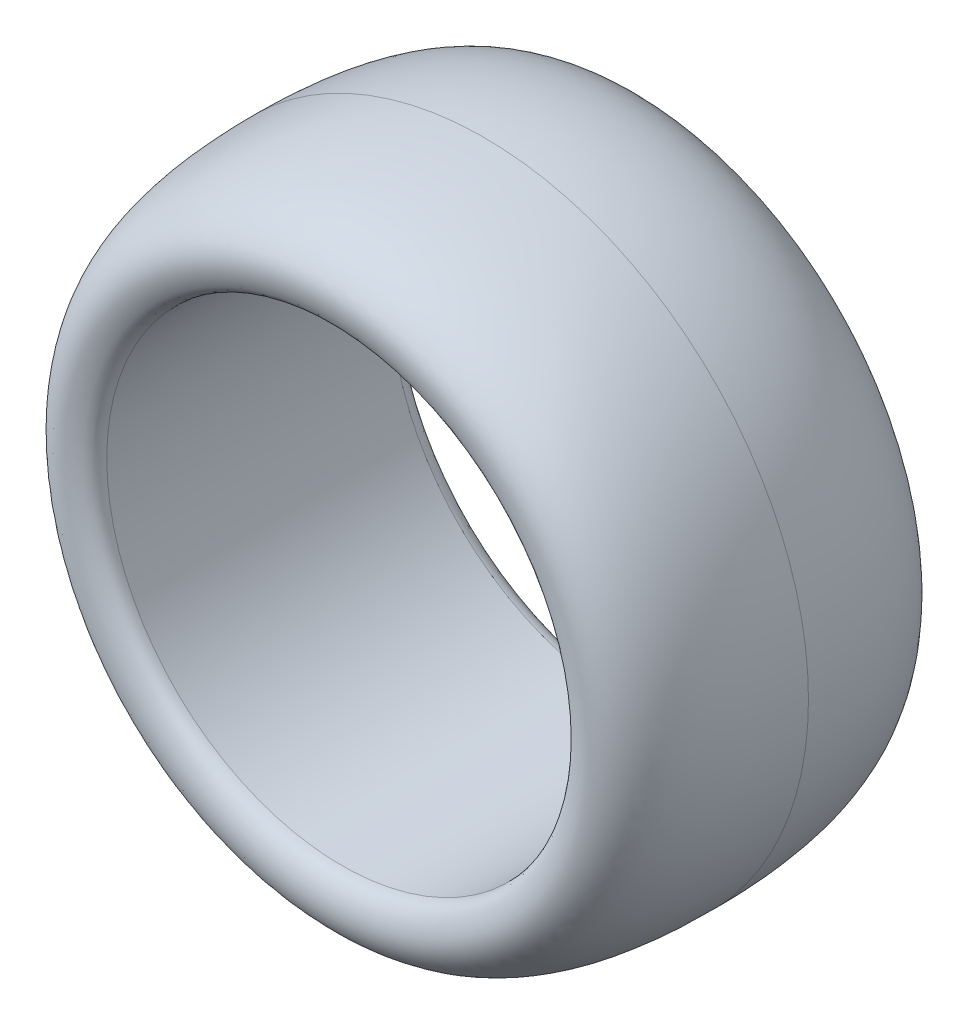
SolidWorks part; units mm, degrees
material "EPDM, dureté 60"
ref_plane "Plan de face" through (0, 0, 0) normal (0, 0, 1) x (1, 0, 0)
ref_plane "Plan de dessus" through (0, 0, 0) normal (0, 1, 0) x (1, 0, 0)
ref_plane "Plan de droite" through (0, 0, 0) normal (1, 0, 0) x (0, 0, -1)
sketch "Esquisse1" plane through (0, 0, 0) normal (1, 0, 0) x (0, 0, -1)
  line L0 (0, 0) -> (0, 29) construction
  line L1 (17.5, 29) -> (-17.5, 29)
  line L2 (-12.9421, 40) -> (0, 40) construction
  line L3 (0, 40) -> (0, 29) construction
  line L4 (0, 0) -> (19.7786, 0) construction
  spline S0 degree 3 poles (-17.5, 29) (-18.4263, 29.1062) (-19.2946, 29.5068) (-20.3501, 34.4072) (-16.1976, 40.0211) (0, 40) knots 0 0 0 0 0.431477 0.531477 1 1 1 1
  spline S1 degree 3 poles (17.5, 29) (18.4263, 29.1062) (19.2946, 29.5068) (20.3501, 34.4072) (16.1976, 40.0211) (0, 40) knots 0 0 0 0 0.431477 0.531477 1 1 1 1
  dimension "D1" = 17.5
  dimension "D2" = 29
  dimension "D3" = 40
  dimension "D4" = 19.7786
  dimension "D5" = 31.8566
revolve "Révolution1" add sketch "Esquisse1" angle 360 about L4
